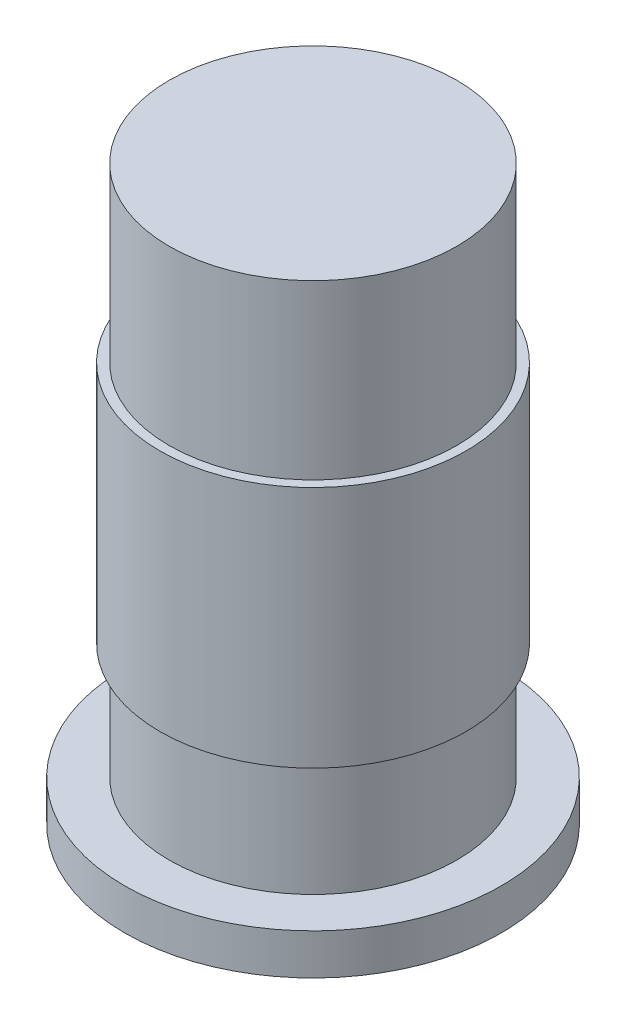
SolidWorks part; units mm, degrees
ref_plane "Alzado" through (0, 0, 0) normal (0, 0, 1) x (1, 0, 0)
ref_plane "Planta" through (0, 0, 0) normal (0, 1, 0) x (1, 0, 0)
ref_plane "Vista lateral" through (0, 0, 0) normal (1, 0, 0) x (0, 0, -1)
sketch "Croquis1" plane through (0, 0, 0) normal (0, 1, 0) x (1, 0, 0)
  circle A0 centre (0, 0) radius 101.5
  dimension "D1" = 203
extrude "Saliente-Extruir1" add sketch "Croquis1" along normal blind 22
sketch "Croquis2" plane through (0, 22, 0) normal (0, 1, 0) x (1, 0, 0)
  circle A0 centre (0, 0) radius 77.5
  dimension "D1" = 155
extrude "Saliente-Extruir2" add sketch "Croquis2" along normal blind 286.5
ref_plane "Plano1" through (0, 84.5, 0) normal (0, 1, 0) x (1, 0, 0)
sketch "Croquis3" plane through (0, 84.5, 0) normal (0, 1, 0) x (1, 0, 0)
  circle A0 centre (0, 0) radius 82.5
  dimension "D1" = 165
extrude "Saliente-Extruir3" add sketch "Croquis3" along normal blind 131
